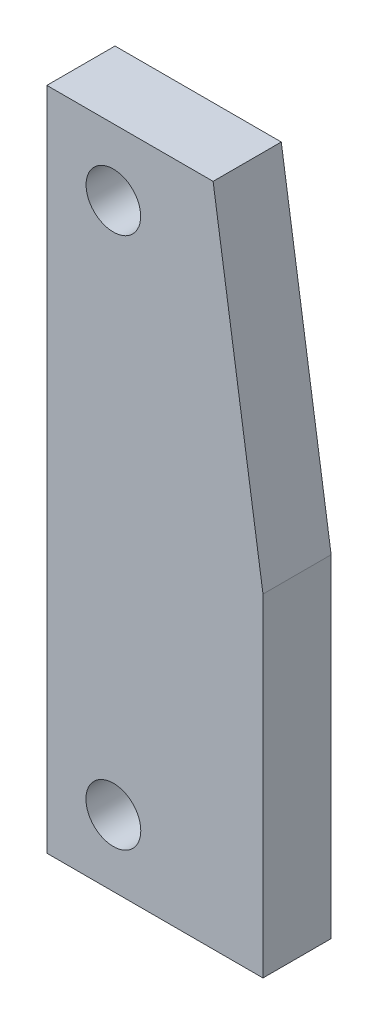
SolidWorks part; units mm, degrees
ref_plane "Front Plane" through (0, 0, 0) normal (0, 0, 1) x (1, 0, 0)
ref_plane "Top Plane" through (0, 0, 0) normal (0, 1, 0) x (1, 0, 0)
ref_plane "Right Plane" through (0, 0, 0) normal (1, 0, 0) x (0, 0, -1)
sketch "Sketch1" plane through (0, 0, 0) normal (0, 0, 1) x (1, 0, 0)
  line L0 (1, 2.4837) -> (1, 42.4837)
  line L1 (1, 42.4837) -> (11, 42.4837)
  line L2 (41, 42.4837) -> (31, 42.4837) construction
  line L3 (11, 42.4837) -> (14, 22.4837)
  line L4 (14, 22.4837) -> (14, 2.4837)
  line L5 (41, 2.4837) -> (28, 2.4837) construction
  line L6 (14, 2.4837) -> (1, 2.4837)
  circle A0 centre (5, 6.4837) radius 1.65
  circle A1 centre (5, 38.4837) radius 1.6425
  dimension "D1" = 10
  dimension "D2" = 13
extrude "Boss-Extrude1" add sketch "Sketch1" along normal blind 4.1
ref_plane "Plane1" through (21, 0, 0) normal (1, 0, 0) x (0, 0, -1)
